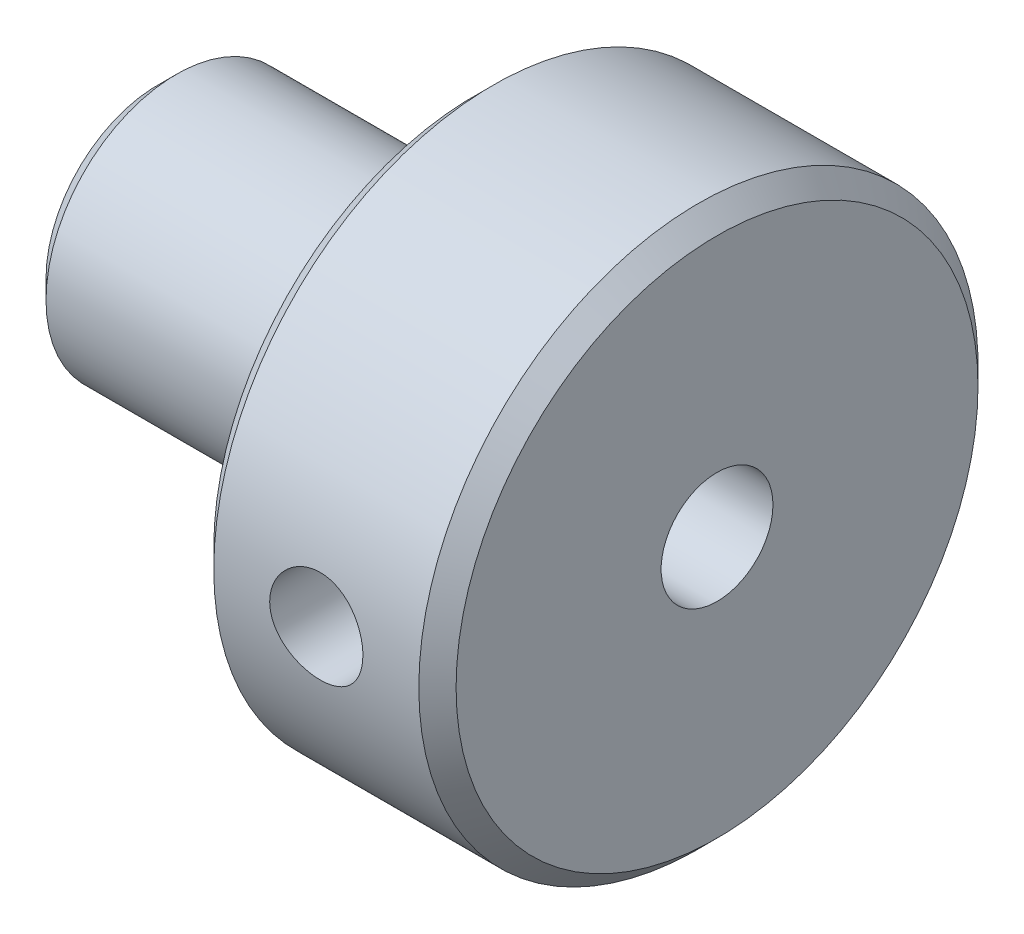
SolidWorks part; units mm, degrees
ref_plane "Ebene vorne" through (0, 0, 0) normal (0, 0, 1) x (1, 0, 0)
ref_plane "Ebene oben" through (0, 0, 0) normal (0, 1, 0) x (1, 0, 0)
ref_plane "Ebene rechts" through (0, 0, 0) normal (1, 0, 0) x (0, 0, -1)
sketch "Sketch1" plane through (0, 0, 0) normal (0, 0, 1) x (1, 0, 0)
  line L0 (0, 0) -> (17.9472, 0) construction
  line L1 (0, 0) -> (0, 3.5)
  line L2 (0, 3.5) -> (8.5, 3.5)
  line L3 (8.5, 3.5) -> (8.5, 7.5)
  line L4 (8.5, 7.5) -> (15, 7.5)
  line L5 (15, 7.5) -> (15, 0)
  line L6 (0, 0) -> (15, 0)
  dimension "D1" = 7
  dimension "D2" = 8.5
  dimension "D3" = 15
  dimension "D4" = 6.5
revolve "Revolve1" add sketch "Sketch1" angle 360 about L0
hole_wizard "M3 Tapped Hole1" positions "Sketch3" profile "Sketch2" tap size "M3" standard "DIN"
sketch "Sketch3" plane through (0, 0, 0) normal (-1, 0, 0) x (0, 0, 1)
  point P0 (0, 0)
sketch "Sketch2" plane through (0, 0, 0) normal (0, 1, 0) x (0, 0, 1)
  line L0 (0, 0) -> (0, 8.7511)
  line L1 (0, 8.7511) -> (1.25, 8)
  line L2 (1.25, 8) -> (1.25, 0)
  line L5 (1.25, 0) -> (0, 0)
  line L10 (0, 8.7511) -> (-1.25, 8) construction
  line L11 (0, -6.35) -> (0, 107.95) construction
  dimension "Tap Drill Dia." = 2.5
  dimension "Tap Drill Depth" = 8
  dimension "Drill Angle" = 118
cosmetic thread "Hole Thread1" parameters "D1"=8, "D2"=3
hole_wizard "Ø3.0 (3) Diameter Hole1" positions "Sketch5" profile "Sketch6" hole size "Ø3.0" standard "DIN"
sketch "Sketch5" plane through (15, 0, 0) normal (1, 0, 0) x (0, 0, -1)
  point P0 (0, 0)
sketch "Sketch6" plane through (15, 0, 0) normal (0, 1, 0) x (0, 0, -1)
  line L0 (0, 0) -> (0, 3.9013)
  line L1 (0, 3.9013) -> (1.5, 3)
  line L2 (1.5, 3) -> (1.5, 0)
  line L5 (1.5, 0) -> (0, 0)
  line L10 (0, 3.9013) -> (-1.5, 3) construction
  line L11 (0, -6.35) -> (0, 107.95) construction
  dimension "Hole Dia." = 3
  dimension "Hole Depth" = 3
  dimension "Drill Angle" = 118
ref_plane "Plane1" through (0, 0, 7.5) normal (0, 0, 1) x (1, 0, 0)
hole_wizard "M3 Tapped Hole2" positions "Sketch8" profile "Sketch9" tap size "M3" standard "DIN"
sketch "Sketch8" plane through (0, 0, 7.5) normal (0, 0, 1) x (1, 0, 0)
  line L0 (11.75, 0) -> (11.75, 4.6494) construction
  line L2 (15, -7.5) -> (15, 7.5) construction
  line L3 (8.5, 7.5) -> (8.5, -7.5) construction
  point P0 (11.75, 0)
sketch "Sketch9" plane through (11.75, 0, 7.5) normal (1, 0, 0) x (0, -1, 0)
  line L0 (0, 0) -> (0, 12.7511)
  line L1 (0, 12.7511) -> (1.25, 12)
  line L2 (1.25, 12) -> (1.25, 0)
  line L5 (1.25, 0) -> (0, 0)
  line L10 (0, 12.7511) -> (-1.25, 12) construction
  line L11 (0, -6.35) -> (0, 107.95) construction
  dimension "Tap Drill Dia." = 2.5
  dimension "Tap Drill Depth" = 12
  dimension "Drill Angle" = 118
cosmetic thread "Hole Thread2" parameters "D1"=8, "D2"=3
chamfer "Chamfer1" distance 0.5 angle 45 3 edges at (0, 0, 3.5) (8.5, 0, 7.5) (15, 0, 7.5)
